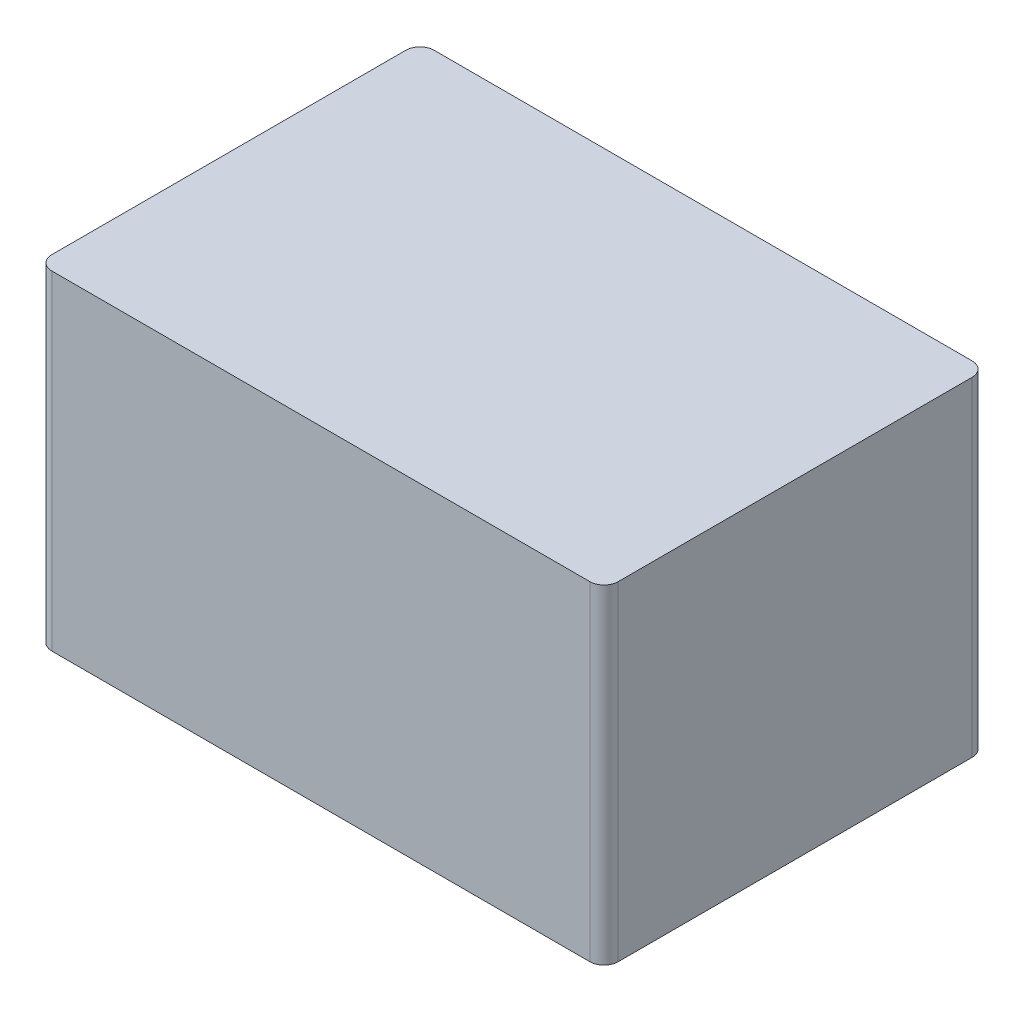
SolidWorks part; units mm, degrees
ref_plane "Front Plane" through (0, 0, 0) normal (0, 0, 1) x (1, 0, 0)
ref_plane "Top Plane" through (0, 0, 0) normal (0, 1, 0) x (1, 0, 0)
ref_plane "Right Plane" through (0, 0, 0) normal (1, 0, 0) x (0, 0, -1)
sketch "Sketch1" plane through (0, 0, 0) normal (0, 1, 0) x (1, 0, 0)
  line L1 (0, 0) -> (80, 0)
  line L2 (0, 0) -> (0, 54)
  line L3 (0, 54) -> (80, 54)
  line L4 (80, 0) -> (80, 54)
  dimension "D1" = 80
  dimension "D2" = 54
extrude "Boss-Extrude2" add sketch "Sketch1" along normal blind 46.5
fillet "Fillet1" radius 2 4 edges at (0, 23.25, -54) (0, 23.25, 0) (80, 23.25, -54) (80, 23.25, 0)
